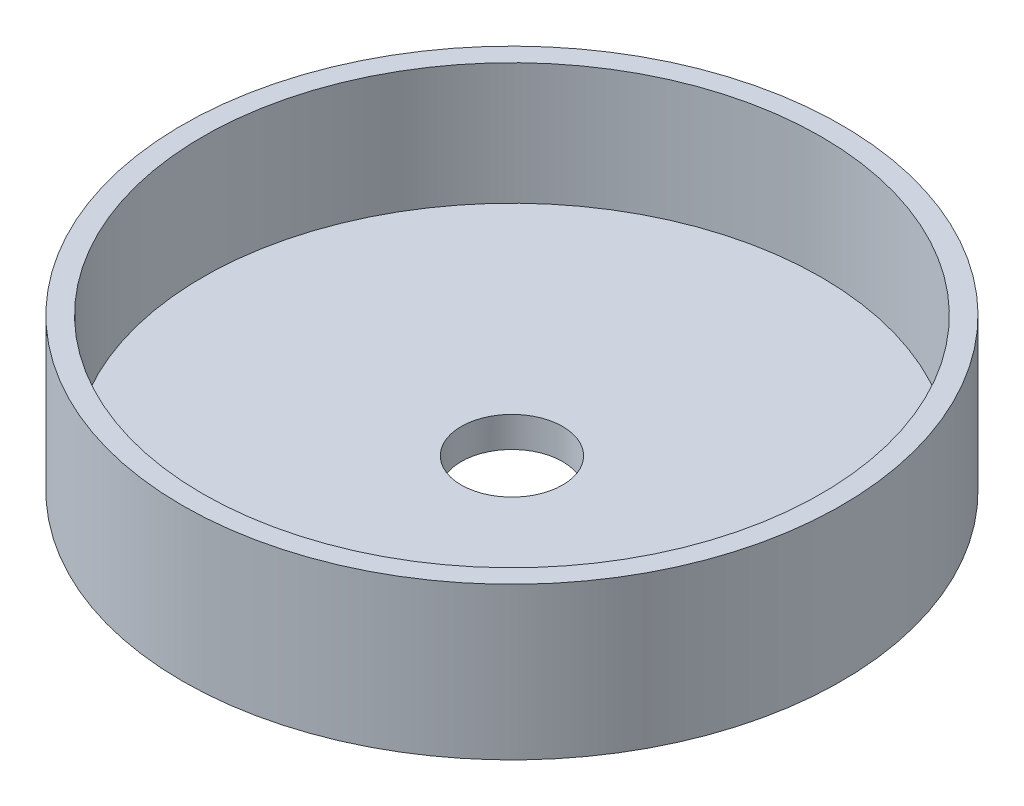
SolidWorks part; units mm, degrees
ref_plane "Front Plane" through (0, 0, 0) normal (0, 0, 1) x (1, 0, 0)
ref_plane "Top Plane" through (0, 0, 0) normal (0, 1, 0) x (1, 0, 0)
ref_plane "Right Plane" through (0, 0, 0) normal (1, 0, 0) x (0, 0, -1)
sketch "Çizim1" plane through (0, 0, 0) normal (0, 1, 0) x (1, 0, 0)
  circle A0 centre (0, 0) radius 32.5
extrude "Yükseklik-Ekstrüzyon2" add sketch "Çizim1" along normal blind 15 contours A0
sketch "Çizim3" plane through (0, 15, 0) normal (0, 1, 0) x (1, 0, 0)
  circle A1 centre (0, 0) radius 30.5
extrude "Kes-Ekstrüzyon1" cut sketch "Çizim3" against normal blind 12
sketch "Çizim4" plane through (0, 0, 0) normal (0, -1, 0) x (1, 0, 0)
  circle A0 centre (0, 0) radius 5
extrude "Kes-Ekstrüzyon2" cut sketch "Çizim4" against normal blind 12
